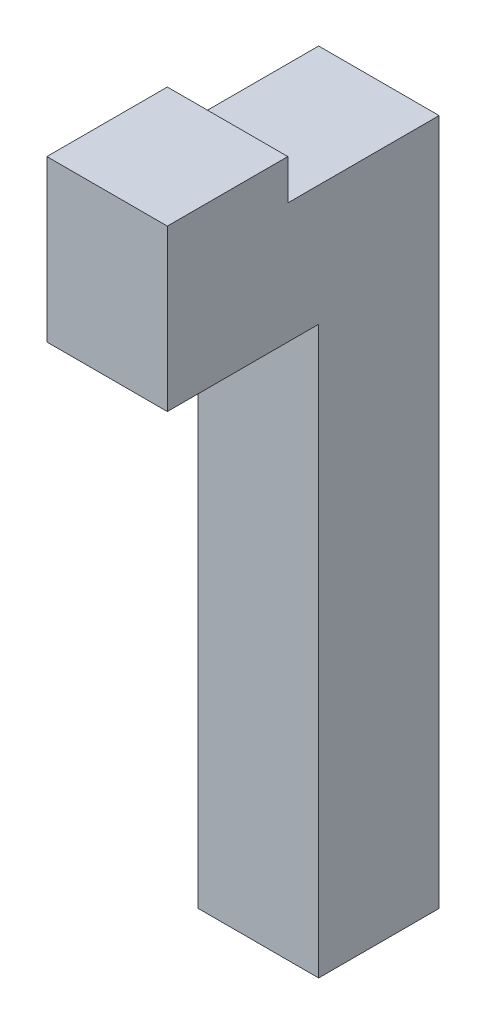
SolidWorks part; units mm, degrees
ref_plane "Front Plane" through (0, 0, 0) normal (0, 0, 1) x (1, 0, 0)
ref_plane "Top Plane" through (0, 0, 0) normal (0, 1, 0) x (1, 0, 0)
ref_plane "Right Plane" through (0, 0, 0) normal (1, 0, 0) x (0, 0, -1)
sketch "Sketch1" plane through (0, 0, 0) normal (0, 1, 0) x (1, 0, 0)
  line L1 (-15, 15) -> (15, 15)
  line L2 (-15, 15) -> (-15, -15)
  line L3 (-15, -15) -> (15, -15)
  line L4 (15, 15) -> (15, -15)
  line L5 (-15, 15) -> (15, -15) construction
  line L6 (-15, -15) -> (15, 15) construction
  point P0 (0, 0)
  dimension "D1" = 30
  dimension "D2" = 30
extrude "Boss-Extrude1" add sketch "Sketch1" along normal blind 171
sketch "Sketch2" plane through (0, 0, 0) normal (0, -1, 0) x (1, 0, 0)
  circle A0 centre (0, 0) radius 10
  dimension "D1" = 20
extrude "Cut-Extrude1" cut sketch "Sketch2" against normal blind 10
sketch "Sketch3" plane through (0, 0, 15) normal (0, 0, 1) x (1, 0, 0)
  line L1 (-15, 171) -> (15, 171)
  line L2 (-15, 171) -> (-15, 141)
  line L3 (-15, 141) -> (15, 141)
  line L4 (15, 171) -> (15, 141)
  dimension "D1" = 30
  dimension "D2" = 30
extrude "Boss-Extrude2" add sketch "Sketch3" along normal blind 37.6839
sketch "Sketch5" plane through (0, 171, 0) normal (0, 1, 0) x (1, 0, 0)
  line L1 (-15, -52.6839) -> (15, -52.6839)
  line L2 (-15, -52.6839) -> (-15, -22.6839)
  line L3 (-15, -22.6839) -> (15, -22.6839)
  line L4 (15, -52.6839) -> (15, -22.6839)
  dimension "D1" = 30
  dimension "D2" = 30
extrude "Boss-Extrude3" add sketch "Sketch5" along normal blind 10
